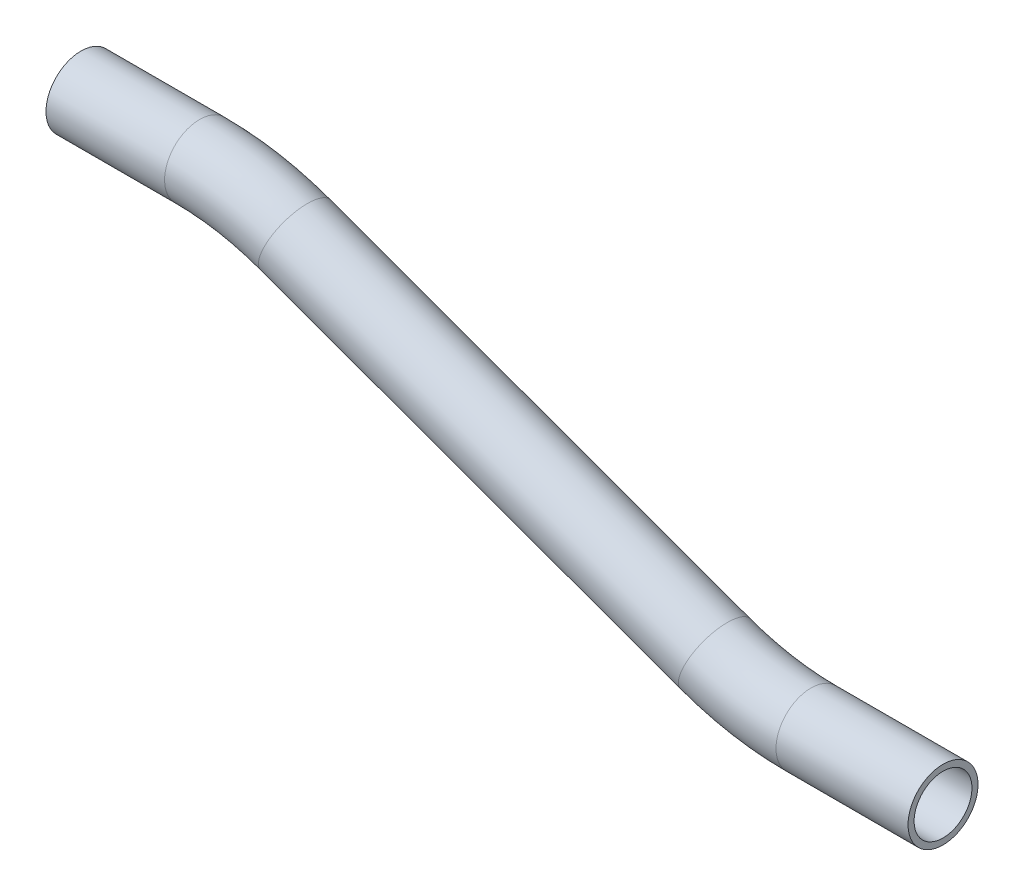
SolidWorks part; units mm, degrees
material "6061 Alloy"
ref_plane "Front Plane" through (0, 0, 0) normal (0, 0, 1) x (1, 0, 0)
ref_plane "Top Plane" through (0, 0, 0) normal (0, 1, 0) x (1, 0, 0)
ref_plane "Right Plane" through (0, 0, 0) normal (1, 0, 0) x (0, 0, -1)
sketch "Sketch1" plane through (0, 0, 0) normal (0, 0, 1) x (1, 0, 0)
  line L0 (29.8322, -12.2) -> (62.1161, -12.2)
  line L1 (88.178, -16.7954) -> (202.4982, -58.4045)
  line L2 (228.5602, -63) -> (264.5016, -63)
  line L3 (228.5602, -63) -> (76.0924, -63) construction
  line L4 (88.178, -16.7954) -> (202.4982, -58.4045) construction
  line L5 (202.4982, -58.4045) -> (282.0836, -87.3713) construction
  line L6 (202.4982, -58.4045) -> (88.178, -16.7954) construction
  line L7 (88.178, -16.7954) -> (-104.6523, 53.3891) construction
  line L8 (29.8322, -12.2) -> (62.1161, -12.2) construction
  line L9 (62.1161, -12.2) -> (185.9661, -12.2) construction
  arc A0 (62.1161, -12.2) -> (88.178, -16.7954) centre (62.1161, -88.4) cw
  arc A1 (202.4982, -58.4045) -> (228.5602, -63) centre (228.5602, 13.2) ccw
  point P9 (75.5522, -12.2)
  point P14 (215.124, -63)
  dimension "D1" = 76.2
  dimension "D2" = 76.2
  dimension "D4" = 20
  dimension "D3" = 20
  dimension "D5" = 148.5293
  dimension "D6" = 45.72
  dimension "D7" = 49.3776
ref_plane "Plane1" through (29.8322, -12.2, 0) normal (1, 0, 0) x (0, 0, -1)
sketch "Sketch2" plane through (29.8322, -12.2, 0) normal (1, 0, 0) x (0, 0, -1)
  circle A0 centre (0, 0) radius 9.525
  circle A1 centre (0, 0) radius 7.874
  dimension "D1" = 15.748
  dimension "D2" = 19.05
sweep "Sweep1" add profiles "Sketch2" path "Sketch1"
